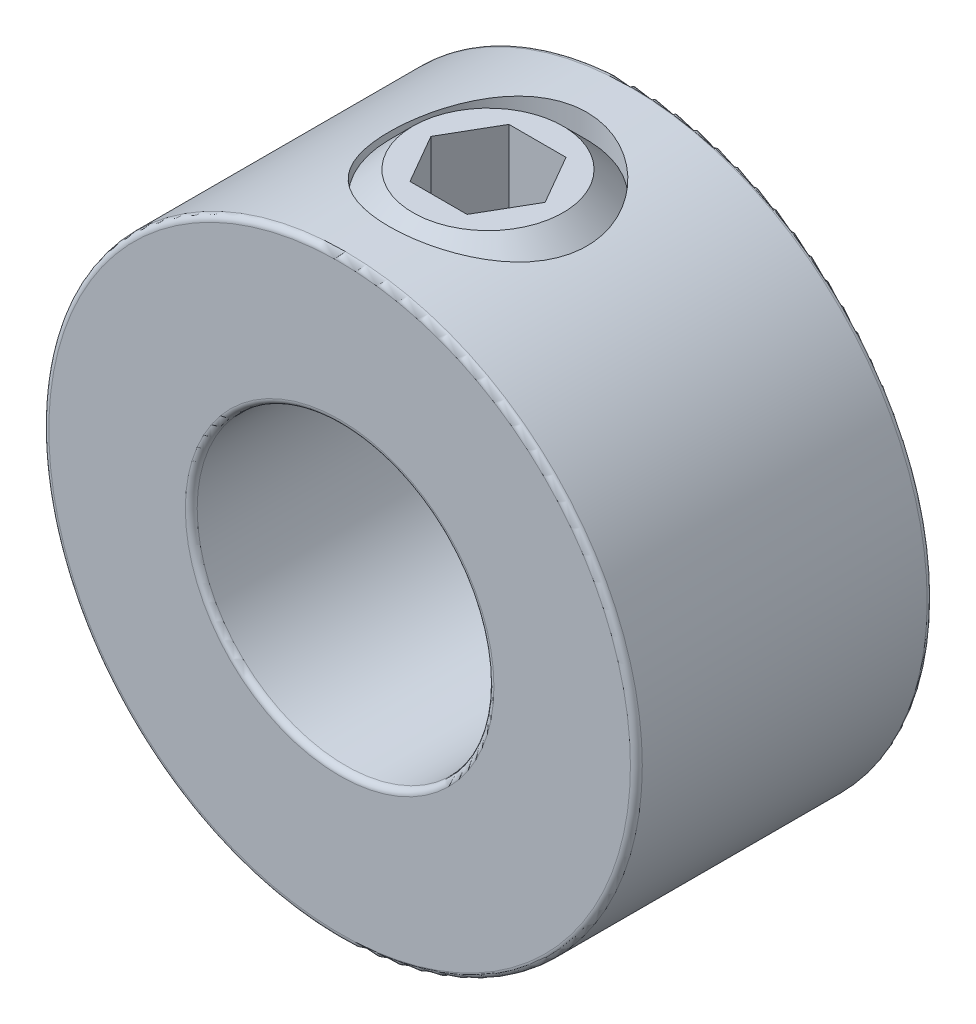
SolidWorks part; units mm, degrees
material "AISI 1045 Steel, cold drawn"
ref_plane "Front Plane" through (0, 0, 0) normal (0, 0, 1) x (1, 0, 0)
ref_plane "Top Plane" through (0, 0, 0) normal (0, 1, 0) x (1, 0, 0)
ref_plane "Right Plane" through (0, 0, 0) normal (1, 0, 0) x (0, 0, -1)
sketch "Sketch1" plane through (0, 0, 0) normal (0, 0, 1) x (1, 0, 0)
  circle A0 centre (0, 0) radius 9.525
  circle A1 centre (0, 0) radius 4.7625
  point P4 (9.525, 0)
  dimension "Bore Dia" = 9.525
  dimension "OD" = 19.05
extrude "Extrude1" add sketch "Sketch1" along normal mid plane 9.525
sketch "Sketch2" plane through (41.275, 0, 0) normal (0, -1, 0) x (0, 0, -1)
  line L0 (4.7625, -41.275) -> (-4.7625, -41.275) construction
  line L1 (-4.7625, -31.75) -> (-4.7625, -50.8) construction
  line L2 (4.7625, -50.8) -> (4.7625, -31.75) construction
  circle A0 centre (0, -41.275) radius 3.175
  point P7 (0, -44.45)
  dimension "Set Screw Dia" = 6.35
extrude "Cut-Extrude1" cut sketch "Sketch2" against normal through all
fillet "Fillet1" radius 0.1905 4 edges at (4.7625, 0, -4.7625) (4.7625, 0, 4.7625) (9.525, 0, -4.7625) (9.525, 0, 4.7625)
sketch "Sketch3" plane through (0, 0, 0) normal (0, 0, 1) x (1, 0, 0)
  line L0 (-2.4082, 4.7625) -> (-0.9202, 4.7625)
  line L1 (0, 5.6827) -> (-0.9202, 4.7625)
  line L2 (0, 5.6827) -> (0, 9.525)
  line L3 (0, 9.525) -> (-2.4082, 9.525)
  line L4 (-3.175, 5.5293) -> (-3.175, 8.7582)
  line L5 (0, 4.7625) -> (0, 0) construction
  line L6 (-3.175, 5.5293) -> (-3.175, 4.7625) construction
  line L7 (-3.175, 4.7625) -> (-2.4082, 4.7625) construction
  line L8 (-3.175, 8.7582) -> (-3.175, 9.525) construction
  line L9 (-2.4082, 4.7625) -> (-3.175, 5.5293)
  line L10 (-3.175, 8.7582) -> (-2.4082, 9.525)
  line L11 (-3.175, 9.525) -> (-2.4082, 9.525) construction
  line L12 (-0.9202, 4.7625) -> (0, 4.7625) construction
  line L13 (0, 4.7625) -> (0, 5.6827) construction
  circle A1 centre (0, 0) radius 4.7625 construction
  dimension "D1" = 0.9202
  dimension "D2" = 0.7668
  dimension "Screw Length" = 4.7625
revolve "Revolve1" add sketch "Sketch3" angle 360 about L5
sketch "Sketch4" plane through (3.3734, 9.525, 0) normal (0, -1, 0) x (0, 0, -1)
  line L1 (0, -1.5404) -> (-1.5875, -2.4569)
  line L2 (-1.5875, -2.4569) -> (-1.5875, -4.29)
  line L3 (-1.5875, -4.29) -> (0, -5.2065)
  line L4 (0, -5.2065) -> (1.5875, -4.29)
  line L5 (1.5875, -4.29) -> (1.5875, -2.4569)
  line L6 (1.5875, -2.4569) -> (0, -1.5404)
  circle A0 centre (0, -3.3734) radius 1.5875 construction
  circle A1 centre (0, -3.3734) radius 1.8331 construction
  dimension "D1" = 3.6662
  dimension "Hex Size" = 3.175
extrude "Cut-Extrude2" cut sketch "Sketch4" along normal blind 3.175
equation "\"D1@Fillet1\" = \"OD@Sketch1\"*.01"
equation "\"D1@Cut-Extrude2\" = \"Hex Size@Sketch4\""
equation "\"D2@Sketch3\" =(\"Set Screw Dia@Sketch2\"-\"D1@Sketch4\")/3.5"
equation "\"D1@Sketch3\" = \"D2@Sketch3\"*1.2"
